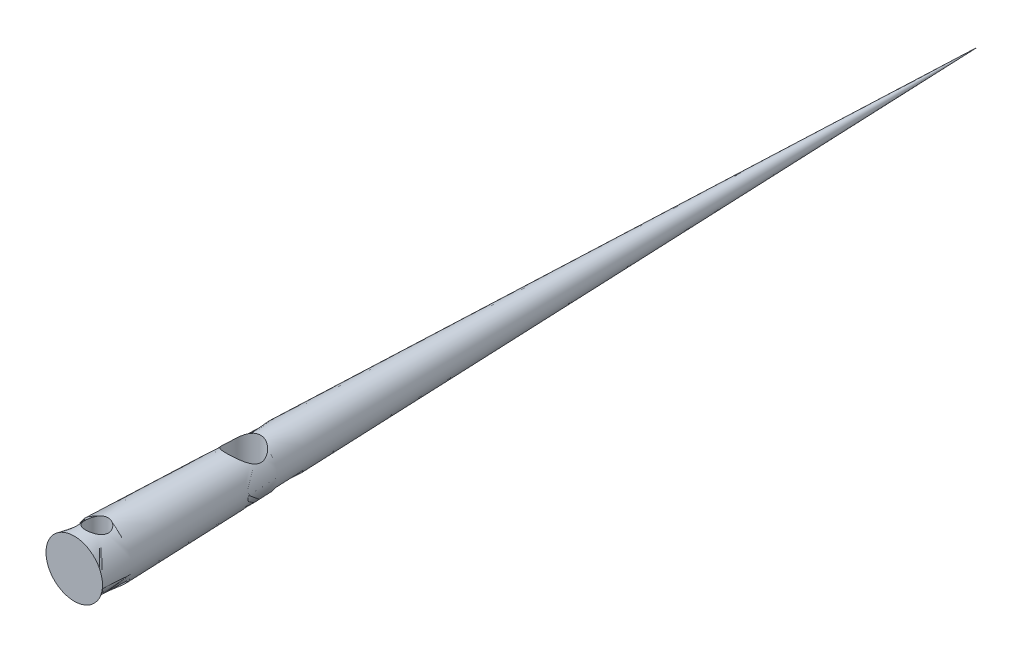
SolidWorks part; units mm, degrees
ref_plane "Front Plane" through (0, 0, 0) normal (0, 0, 1) x (1, 0, 0)
ref_plane "Top Plane" through (0, 0, 0) normal (0, 1, 0) x (1, 0, 0)
ref_plane "Right Plane" through (0, 0, 0) normal (1, 0, 0) x (0, 0, -1)
sketch "Sketch2" plane through (0, 0, 0) normal (0, 1, 0) x (1, 0, 0)
  line L0 (0, 0) -> (2.5, 0)
  line L1 (2.5, 0) -> (0, 80)
  line L2 (0, 80) -> (0, 0)
  dimension "D1" = 2.5
  dimension "D2" = 80
sketch "Sketch3" plane through (0, 0, 0) normal (0, 1, 0) x (1, 0, 0)
  line L0 (0, 0) -> (0, 96.9965) construction
revolve "Revolve2" add sketch "Sketch2" angle 360 about L2
sketch "Sketch4" plane through (0, 0, 0) normal (0, 1, 0) x (1, 0, 0)
  line L0 (0, 0) -> (0, 96.9965) construction
  circle A0 centre (0, 15) radius 1.5
  dimension "D1" = 3
  dimension "D2" = 15
extrude "Cut-Extrude3" cut sketch "Sketch4" against normal through all both and the other way through all
sketch "Sketch7" plane through (0, 0, 0) normal (0, 1, 0) x (1, 0, 0)
  line L0 (-2.5, 0) -> (2.5, 0) construction
  circle A0 centre (0, 2) radius 1
  dimension "D1" = 2
  dimension "D2" = 2
extrude "Cut-Extrude4" cut sketch "Sketch7" against normal through all both and the other way through all
